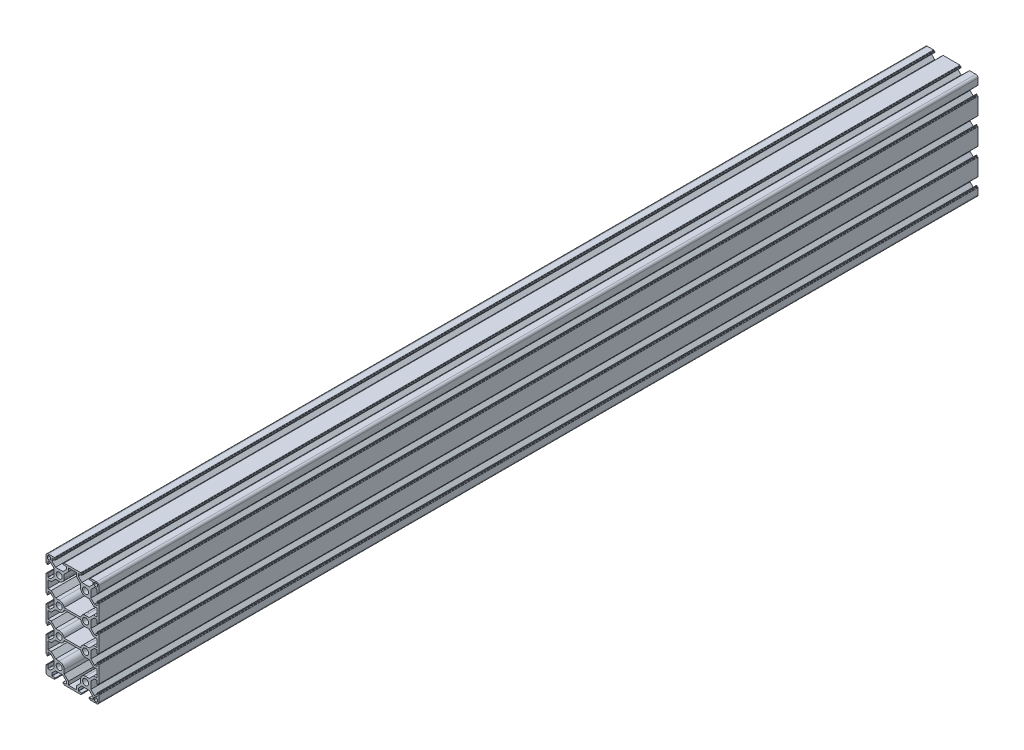
SolidWorks part; units mm, degrees
material "6063 T5"
ref_plane "Спереди" through (0, 0, 0) normal (0, 0, 1) x (1, 0, 0)
ref_plane "Сверху" through (0, 0, 0) normal (0, 1, 0) x (1, 0, 0)
ref_plane "Справа" through (0, 0, 0) normal (1, 0, 0) x (0, 0, -1)
sketch "Эскиз1" plane through (0, 0, 0) normal (0, 0, 1) x (1, 0, 0)
  line L0 (-34.4622, 45.0307) -> (-34.4622, -44.9693) construction
  line L1 (0, 45) -> (0, -45) construction
  line L2 (30, 0) -> (-30, 0) construction
  line L3 (-30, 38.25) -> (-30, 42.5)
  line L4 (-27.5, 45) -> (-23.25, 45)
  line L5 (4.5, 42.8) -> (-4.5, 42.8)
  line L6 (-27.35, 43.55) -> (-25.95, 43.55)
  line L7 (-28.55, 42.35) -> (-28.55, 40.95)
  line L8 (-27.35, 39.75) -> (-25.95, 39.75)
  line L9 (-24.75, 42.35) -> (-24.75, 40.95)
  line L10 (-4.5, 42.8) -> (-4.5, 38.9059)
  line L11 (-4.5, 38.9059) -> (-9.3, 34.1059)
  line L12 (-9.3, 34.1059) -> (-9.3, 30)
  line L13 (-15, 24.3) -> (-19.1059, 24.3)
  line L14 (-19.1059, 24.3) -> (-24.0559, 19.35)
  line L15 (-24.0559, 19.35) -> (-27.8, 19.35)
  line L16 (-27.8, 19.35) -> (-27.8, 10.65)
  line L17 (-27.8, 10.65) -> (-24.0559, 10.65)
  line L18 (-24.0559, 10.65) -> (-19.1059, 5.7)
  line L19 (-19.1059, 5.7) -> (-15, 5.7)
  line L20 (-9.4071, 1.1) -> (9.4071, 1.1)
  line L21 (-6.75, 45) -> (6.75, 45)
  line L22 (-30, 21.75) -> (-30, 8.25)
  line L23 (30, 21.75) -> (30, 8.25)
  line L24 (27.5, 45) -> (23.25, 45)
  line L25 (30, 38.25) -> (30, 42.5)
  line L26 (19.1059, 5.7) -> (15, 5.7)
  line L27 (24.0559, 10.65) -> (19.1059, 5.7)
  line L28 (27.8, 10.65) -> (24.0559, 10.65)
  line L29 (27.8, 19.35) -> (27.8, 10.65)
  line L30 (24.0559, 19.35) -> (27.8, 19.35)
  line L31 (19.1059, 24.3) -> (24.0559, 19.35)
  line L32 (15, 24.3) -> (19.1059, 24.3)
  line L33 (9.3, 34.1059) -> (9.3, 30)
  line L34 (4.5, 38.9059) -> (9.3, 34.1059)
  line L35 (4.5, 42.8) -> (4.5, 38.9059)
  line L36 (27.35, 43.55) -> (25.95, 43.55)
  line L37 (28.55, 42.35) -> (28.55, 40.95)
  line L38 (27.35, 39.75) -> (25.95, 39.75)
  line L39 (24.75, 42.35) -> (24.75, 40.95)
  line L40 (-9.4071, -28.9) -> (9.4071, -28.9)
  line L41 (30, -15) -> (45, -15) construction
  line L46 (30, -21.75) -> (30, -8.25)
  line L47 (-30, -21.75) -> (-30, -8.25)
  line L48 (-27.5, -75) -> (-23.25, -75)
  line L54 (15, -24.3) -> (19.1059, -24.3)
  line L55 (19.1059, -24.3) -> (24.0559, -19.35)
  line L56 (24.0559, -19.35) -> (27.8, -19.35)
  line L57 (27.8, -19.35) -> (27.8, -10.65)
  line L58 (27.8, -10.65) -> (24.0559, -10.65)
  line L59 (24.0559, -10.65) -> (19.1059, -5.7)
  line L60 (19.1059, -5.7) -> (15, -5.7)
  line L61 (-9.4071, -1.1) -> (9.4071, -1.1)
  line L62 (-19.1059, -5.7) -> (-15, -5.7)
  line L63 (-24.0559, -10.65) -> (-19.1059, -5.7)
  line L64 (-27.8, -10.65) -> (-24.0559, -10.65)
  line L65 (-27.8, -19.35) -> (-27.8, -10.65)
  line L66 (-24.0559, -19.35) -> (-27.8, -19.35)
  line L67 (-19.1059, -24.3) -> (-24.0559, -19.35)
  line L68 (-15, -24.3) -> (-19.1059, -24.3)
  line L75 (-30, -68.25) -> (-30, -72.5)
  line L76 (28.55, -72.35) -> (28.55, -70.95)
  line L77 (27.35, -73.55) -> (25.95, -73.55)
  line L78 (24.75, -72.35) -> (24.75, -70.95)
  line L79 (27.35, -69.75) -> (25.95, -69.75)
  line L80 (27.5, -75) -> (23.25, -75)
  line L81 (30, -68.25) -> (30, -72.5)
  line L82 (-6.75, -75) -> (6.75, -75)
  line L83 (27.8, -40.65) -> (24.0559, -40.65)
  line L84 (27.8, -49.35) -> (27.8, -40.65)
  line L85 (24.0559, -49.35) -> (27.8, -49.35)
  line L86 (19.1059, -54.3) -> (24.0559, -49.35)
  line L87 (15, -54.3) -> (19.1059, -54.3)
  line L88 (9.3, -64.1059) -> (9.3, -60)
  line L89 (4.5, -68.9059) -> (9.3, -64.1059)
  line L90 (4.5, -72.8) -> (4.5, -68.9059)
  line L91 (4.5, -72.8) -> (-4.5, -72.8)
  line L92 (-4.5, -72.8) -> (-4.5, -68.9059)
  line L93 (-4.5, -68.9059) -> (-9.3, -64.1059)
  line L94 (-9.3, -64.1059) -> (-9.3, -60)
  line L95 (-15, -54.3) -> (-19.1059, -54.3)
  line L96 (-19.1059, -54.3) -> (-24.0559, -49.35)
  line L97 (-24.0559, -49.35) -> (-27.8, -49.35)
  line L98 (-27.8, -49.35) -> (-27.8, -40.65)
  line L99 (-27.8, -40.65) -> (-24.0559, -40.65)
  line L100 (-24.0559, -40.65) -> (-19.1059, -35.7)
  line L101 (-19.1059, -35.7) -> (-15, -35.7)
  line L102 (-9.4071, -31.1) -> (9.4071, -31.1)
  line L103 (19.1059, -35.7) -> (15, -35.7)
  line L104 (24.0559, -40.65) -> (19.1059, -35.7)
  line L105 (-30, -51.75) -> (-30, -38.25)
  line L106 (30, -51.75) -> (30, -38.25)
  arc A0 (-30, 42.5) -> (-27.5, 45) centre (-27.5, 42.5) cw
  arc A1 (-28.55, 40.95) -> (-27.35, 39.75) centre (-27.35, 40.95) ccw
  arc A2 (-25.95, 39.75) -> (-24.75, 40.95) centre (-25.95, 40.95) ccw
  arc A3 (-25.95, 43.55) -> (-24.75, 42.35) centre (-25.95, 42.35) cw
  arc A4 (-27.35, 43.55) -> (-28.55, 42.35) centre (-27.35, 42.35) ccw
  circle A5 centre (-15, 30) radius 3.4
  arc A6 (-9.3, 30) -> (-15, 24.3) centre (-15, 30) cw
  arc A7 (-15, 5.7) -> (-9.4071, 1.1) centre (-15, 0) cw
  circle A8 centre (-15, 0) radius 3.4
  arc A9 (30, 42.5) -> (27.5, 45) centre (27.5, 42.5) ccw
  arc A10 (15, 5.7) -> (9.4071, 1.1) centre (15, 0) ccw
  arc A11 (9.3, 30) -> (15, 24.3) centre (15, 30) ccw
  circle A12 centre (15, 30) radius 3.4
  circle A13 centre (15, 0) radius 3.4
  arc A14 (25.95, 43.55) -> (24.75, 42.35) centre (25.95, 42.35) ccw
  arc A15 (27.35, 43.55) -> (28.55, 42.35) centre (27.35, 42.35) cw
  arc A16 (28.55, 40.95) -> (27.35, 39.75) centre (27.35, 40.95) cw
  arc A17 (25.95, 39.75) -> (24.75, 40.95) centre (25.95, 40.95) cw
  arc A18 (-15, -24.3) -> (-9.4071, -28.9) centre (-15, -30) cw
  circle A23 centre (-15, -30) radius 3.4
  circle A24 centre (15, -30) radius 3.4
  arc A26 (15, -5.7) -> (9.4071, -1.1) centre (15, 0) cw
  arc A27 (-15, -5.7) -> (-9.4071, -1.1) centre (-15, 0) ccw
  arc A33 (15, -24.3) -> (9.4071, -28.9) centre (15, -30) ccw
  arc A34 (-30, -72.5) -> (-27.5, -75) centre (-27.5, -72.5) ccw
  arc A35 (28.55, -70.95) -> (27.35, -69.75) centre (27.35, -70.95) ccw
  arc A36 (27.35, -73.55) -> (28.55, -72.35) centre (27.35, -72.35) ccw
  arc A37 (25.95, -73.55) -> (24.75, -72.35) centre (25.95, -72.35) cw
  arc A38 (25.95, -69.75) -> (24.75, -70.95) centre (25.95, -70.95) ccw
  arc A39 (30, -72.5) -> (27.5, -75) centre (27.5, -72.5) cw
  arc A40 (9.3, -60) -> (15, -54.3) centre (15, -60) cw
  arc A41 (-9.3, -60) -> (-15, -54.3) centre (-15, -60) ccw
  arc A42 (-15, -35.7) -> (-9.4071, -31.1) centre (-15, -30) ccw
  arc A43 (15, -35.7) -> (9.4071, -31.1) centre (15, -30) cw
  circle A44 centre (-15, -60) radius 3.4
  circle A45 centre (15, -60) radius 3.4
  point P22 (-24.75, 43.55)
  point P25 (-28.55, 43.55)
  point P63 (0, 1.1)
  point P72 (0, 42.8)
  point P174 (47.9891, -15)
  point P175 (-4.5, 38.9059)
  line B0 (-30, 8.25) -> (-30, 5.5)
  line B1 (-29.7, 5.2) -> (-29.3, 5.2)
  line B2 (-29, 4.9) -> (-29, 4.4)
  line B3 (-28.7, 4.1) -> (-28.3, 4.1)
  line B4 (-28, 4.4) -> (-28, 7.95)
  line B5 (-27.7, 8.25) -> (-25.05, 8.25)
  line B6 (-25.05, 8.25) -> (-21, 4.2)
  line B7 (-21, 0) -> (-30, 0) construction
  line B8 (-21, -4.2) -> (-21, 4.2)
  line B9 (-25.05, -8.25) -> (-21, -4.2)
  line B10 (-27.7, -8.25) -> (-25.05, -8.25)
  line B11 (-28, -4.4) -> (-28, -7.95)
  line B12 (-28.7, -4.1) -> (-28.3, -4.1)
  line B13 (-29, -4.9) -> (-29, -4.4)
  line B14 (-29.7, -5.2) -> (-29.3, -5.2)
  line B15 (-30, -8.25) -> (-30, -5.5)
  arc B16 (-28, 7.95) -> (-27.7, 8.25) centre (-27.7, 7.95) cw
  arc B17 (-28.3, 4.1) -> (-28, 4.4) centre (-28.3, 4.4) ccw
  arc B18 (-29, 4.4) -> (-28.7, 4.1) centre (-28.7, 4.4) ccw
  arc B19 (-29.3, 5.2) -> (-29, 4.9) centre (-29.3, 4.9) cw
  arc B20 (-30, 5.5) -> (-29.7, 5.2) centre (-29.7, 5.5) ccw
  arc B21 (-30, -5.5) -> (-29.7, -5.2) centre (-29.7, -5.5) cw
  arc B22 (-29.3, -5.2) -> (-29, -4.9) centre (-29.3, -4.9) ccw
  arc B23 (-29, -4.4) -> (-28.7, -4.1) centre (-28.7, -4.4) cw
  arc B24 (-28.3, -4.1) -> (-28, -4.4) centre (-28.3, -4.4) cw
  arc B25 (-28, -7.95) -> (-27.7, -8.25) centre (-27.7, -7.95) ccw
  line B26 (-30, 38.25) -> (-30, 35.5)
  line B27 (-29.7, 35.2) -> (-29.3, 35.2)
  line B28 (-29, 34.9) -> (-29, 34.4)
  line B29 (-28.7, 34.1) -> (-28.3, 34.1)
  line B30 (-28, 34.4) -> (-28, 37.95)
  line B31 (-27.7, 38.25) -> (-25.05, 38.25)
  line B32 (-25.05, 38.25) -> (-21, 34.2)
  line B33 (-21, 30) -> (-30, 30) construction
  line B34 (-21, 25.8) -> (-21, 34.2)
  line B35 (-25.05, 21.75) -> (-21, 25.8)
  line B36 (-27.7, 21.75) -> (-25.05, 21.75)
  line B37 (-28, 25.6) -> (-28, 22.05)
  line B38 (-28.7, 25.9) -> (-28.3, 25.9)
  line B39 (-29, 25.1) -> (-29, 25.6)
  line B40 (-29.7, 24.8) -> (-29.3, 24.8)
  line B41 (-30, 21.75) -> (-30, 24.5)
  arc B42 (-28, 37.95) -> (-27.7, 38.25) centre (-27.7, 37.95) cw
  arc B43 (-28.3, 34.1) -> (-28, 34.4) centre (-28.3, 34.4) ccw
  arc B44 (-29, 34.4) -> (-28.7, 34.1) centre (-28.7, 34.4) ccw
  arc B45 (-29.3, 35.2) -> (-29, 34.9) centre (-29.3, 34.9) cw
  arc B46 (-30, 35.5) -> (-29.7, 35.2) centre (-29.7, 35.5) ccw
  arc B47 (-30, 24.5) -> (-29.7, 24.8) centre (-29.7, 24.5) cw
  arc B48 (-29.3, 24.8) -> (-29, 25.1) centre (-29.3, 25.1) ccw
  arc B49 (-29, 25.6) -> (-28.7, 25.9) centre (-28.7, 25.6) cw
  arc B50 (-28.3, 25.9) -> (-28, 25.6) centre (-28.3, 25.6) cw
  arc B51 (-28, 22.05) -> (-27.7, 21.75) centre (-27.7, 22.05) ccw
  line B52 (-6.75, 45) -> (-9.5, 45)
  line B53 (-9.8, 44.7) -> (-9.8, 44.3)
  line B54 (-10.1, 44) -> (-10.6, 44)
  line B55 (-10.9, 43.7) -> (-10.9, 43.3)
  line B56 (-10.6, 43) -> (-7.05, 43)
  line B57 (-6.75, 42.7) -> (-6.75, 40.05)
  line B58 (-6.75, 40.05) -> (-10.8, 36)
  line B59 (-15, 36) -> (-15, 45) construction
  line B60 (-19.2, 36) -> (-10.8, 36)
  line B61 (-23.25, 40.05) -> (-19.2, 36)
  line B62 (-23.25, 42.7) -> (-23.25, 40.05)
  line B63 (-19.4, 43) -> (-22.95, 43)
  line B64 (-19.1, 43.7) -> (-19.1, 43.3)
  line B65 (-19.9, 44) -> (-19.4, 44)
  line B66 (-20.2, 44.7) -> (-20.2, 44.3)
  line B67 (-23.25, 45) -> (-20.5, 45)
  arc B68 (-7.05, 43) -> (-6.75, 42.7) centre (-7.05, 42.7) cw
  arc B69 (-10.9, 43.3) -> (-10.6, 43) centre (-10.6, 43.3) ccw
  arc B70 (-10.6, 44) -> (-10.9, 43.7) centre (-10.6, 43.7) ccw
  arc B71 (-9.8, 44.3) -> (-10.1, 44) centre (-10.1, 44.3) cw
  arc B72 (-9.5, 45) -> (-9.8, 44.7) centre (-9.5, 44.7) ccw
  arc B73 (-20.5, 45) -> (-20.2, 44.7) centre (-20.5, 44.7) cw
  arc B74 (-20.2, 44.3) -> (-19.9, 44) centre (-19.9, 44.3) ccw
  arc B75 (-19.4, 44) -> (-19.1, 43.7) centre (-19.4, 43.7) cw
  arc B76 (-19.1, 43.3) -> (-19.4, 43) centre (-19.4, 43.3) cw
  arc B77 (-22.95, 43) -> (-23.25, 42.7) centre (-22.95, 42.7) ccw
  line B78 (6.75, 45) -> (9.5, 45)
  line B79 (9.8, 44.7) -> (9.8, 44.3)
  line B80 (10.1, 44) -> (10.6, 44)
  line B81 (10.9, 43.7) -> (10.9, 43.3)
  line B82 (10.6, 43) -> (7.05, 43)
  line B83 (6.75, 42.7) -> (6.75, 40.05)
  line B84 (6.75, 40.05) -> (10.8, 36)
  line B85 (15, 36) -> (15, 45) construction
  line B86 (19.2, 36) -> (10.8, 36)
  line B87 (23.25, 40.05) -> (19.2, 36)
  line B88 (23.25, 42.7) -> (23.25, 40.05)
  line B89 (19.4, 43) -> (22.95, 43)
  line B90 (19.1, 43.7) -> (19.1, 43.3)
  line B91 (19.9, 44) -> (19.4, 44)
  line B92 (20.2, 44.7) -> (20.2, 44.3)
  line B93 (23.25, 45) -> (20.5, 45)
  arc B94 (7.05, 43) -> (6.75, 42.7) centre (7.05, 42.7) ccw
  arc B95 (10.9, 43.3) -> (10.6, 43) centre (10.6, 43.3) cw
  arc B96 (10.6, 44) -> (10.9, 43.7) centre (10.6, 43.7) cw
  arc B97 (9.8, 44.3) -> (10.1, 44) centre (10.1, 44.3) ccw
  arc B98 (9.5, 45) -> (9.8, 44.7) centre (9.5, 44.7) cw
  arc B99 (20.5, 45) -> (20.2, 44.7) centre (20.5, 44.7) ccw
  arc B100 (20.2, 44.3) -> (19.9, 44) centre (19.9, 44.3) cw
  arc B101 (19.4, 44) -> (19.1, 43.7) centre (19.4, 43.7) ccw
  arc B102 (19.1, 43.3) -> (19.4, 43) centre (19.4, 43.3) ccw
  arc B103 (22.95, 43) -> (23.25, 42.7) centre (22.95, 42.7) cw
  line B104 (30, 38.25) -> (30, 35.5)
  line B105 (29.7, 35.2) -> (29.3, 35.2)
  line B106 (29, 34.9) -> (29, 34.4)
  line B107 (28.7, 34.1) -> (28.3, 34.1)
  line B108 (28, 34.4) -> (28, 37.95)
  line B109 (27.7, 38.25) -> (25.05, 38.25)
  line B110 (25.05, 38.25) -> (21, 34.2)
  line B111 (21, 30) -> (30, 30) construction
  line B112 (21, 25.8) -> (21, 34.2)
  line B113 (25.05, 21.75) -> (21, 25.8)
  line B114 (27.7, 21.75) -> (25.05, 21.75)
  line B115 (28, 25.6) -> (28, 22.05)
  line B116 (28.7, 25.9) -> (28.3, 25.9)
  line B117 (29, 25.1) -> (29, 25.6)
  line B118 (29.7, 24.8) -> (29.3, 24.8)
  line B119 (30, 21.75) -> (30, 24.5)
  arc B120 (28, 37.95) -> (27.7, 38.25) centre (27.7, 37.95) ccw
  arc B121 (28.3, 34.1) -> (28, 34.4) centre (28.3, 34.4) cw
  arc B122 (29, 34.4) -> (28.7, 34.1) centre (28.7, 34.4) cw
  arc B123 (29.3, 35.2) -> (29, 34.9) centre (29.3, 34.9) ccw
  arc B124 (30, 35.5) -> (29.7, 35.2) centre (29.7, 35.5) cw
  arc B125 (30, 24.5) -> (29.7, 24.8) centre (29.7, 24.5) ccw
  arc B126 (29.3, 24.8) -> (29, 25.1) centre (29.3, 25.1) cw
  arc B127 (29, 25.6) -> (28.7, 25.9) centre (28.7, 25.6) ccw
  arc B128 (28.3, 25.9) -> (28, 25.6) centre (28.3, 25.6) ccw
  arc B129 (28, 22.05) -> (27.7, 21.75) centre (27.7, 22.05) cw
  line B130 (30, 8.25) -> (30, 5.5)
  line B131 (29.7, 5.2) -> (29.3, 5.2)
  line B132 (29, 4.9) -> (29, 4.4)
  line B133 (28.7, 4.1) -> (28.3, 4.1)
  line B134 (28, 4.4) -> (28, 7.95)
  line B135 (27.7, 8.25) -> (25.05, 8.25)
  line B136 (25.05, 8.25) -> (21, 4.2)
  line B137 (21, 0) -> (30, 0) construction
  line B138 (21, -4.2) -> (21, 4.2)
  line B139 (25.05, -8.25) -> (21, -4.2)
  line B140 (27.7, -8.25) -> (25.05, -8.25)
  line B141 (28, -4.4) -> (28, -7.95)
  line B142 (28.7, -4.1) -> (28.3, -4.1)
  line B143 (29, -4.9) -> (29, -4.4)
  line B144 (29.7, -5.2) -> (29.3, -5.2)
  line B145 (30, -8.25) -> (30, -5.5)
  arc B146 (28, 7.95) -> (27.7, 8.25) centre (27.7, 7.95) ccw
  arc B147 (28.3, 4.1) -> (28, 4.4) centre (28.3, 4.4) cw
  arc B148 (29, 4.4) -> (28.7, 4.1) centre (28.7, 4.4) cw
  arc B149 (29.3, 5.2) -> (29, 4.9) centre (29.3, 4.9) ccw
  arc B150 (30, 5.5) -> (29.7, 5.2) centre (29.7, 5.5) cw
  arc B151 (30, -5.5) -> (29.7, -5.2) centre (29.7, -5.5) ccw
  arc B152 (29.3, -5.2) -> (29, -4.9) centre (29.3, -4.9) cw
  arc B153 (29, -4.4) -> (28.7, -4.1) centre (28.7, -4.4) ccw
  arc B154 (28.3, -4.1) -> (28, -4.4) centre (28.3, -4.4) ccw
  arc B155 (28, -7.95) -> (27.7, -8.25) centre (27.7, -7.95) cw
  line B156 (-30, -38.25) -> (-30, -35.5)
  line B157 (-29.7, -35.2) -> (-29.3, -35.2)
  line B158 (-29, -34.9) -> (-29, -34.4)
  line B159 (-28.7, -34.1) -> (-28.3, -34.1)
  line B160 (-28, -34.4) -> (-28, -37.95)
  line B161 (-27.7, -38.25) -> (-25.05, -38.25)
  line B162 (-25.05, -38.25) -> (-21, -34.2)
  line B163 (-21, -30) -> (-30, -30) construction
  line B164 (-21, -25.8) -> (-21, -34.2)
  line B165 (-25.05, -21.75) -> (-21, -25.8)
  line B166 (-27.7, -21.75) -> (-25.05, -21.75)
  line B167 (-28, -25.6) -> (-28, -22.05)
  line B168 (-28.7, -25.9) -> (-28.3, -25.9)
  line B169 (-29, -25.1) -> (-29, -25.6)
  line B170 (-29.7, -24.8) -> (-29.3, -24.8)
  line B171 (-30, -21.75) -> (-30, -24.5)
  arc B172 (-28, -37.95) -> (-27.7, -38.25) centre (-27.7, -37.95) ccw
  arc B173 (-28.3, -34.1) -> (-28, -34.4) centre (-28.3, -34.4) cw
  arc B174 (-29, -34.4) -> (-28.7, -34.1) centre (-28.7, -34.4) cw
  arc B175 (-29.3, -35.2) -> (-29, -34.9) centre (-29.3, -34.9) ccw
  arc B176 (-30, -35.5) -> (-29.7, -35.2) centre (-29.7, -35.5) cw
  arc B177 (-30, -24.5) -> (-29.7, -24.8) centre (-29.7, -24.5) ccw
  arc B178 (-29.3, -24.8) -> (-29, -25.1) centre (-29.3, -25.1) cw
  arc B179 (-29, -25.6) -> (-28.7, -25.9) centre (-28.7, -25.6) ccw
  arc B180 (-28.3, -25.9) -> (-28, -25.6) centre (-28.3, -25.6) ccw
  arc B181 (-28, -22.05) -> (-27.7, -21.75) centre (-27.7, -22.05) cw
  line B182 (30, -38.25) -> (30, -35.5)
  line B183 (29.7, -35.2) -> (29.3, -35.2)
  line B184 (29, -34.9) -> (29, -34.4)
  line B185 (28.7, -34.1) -> (28.3, -34.1)
  line B186 (28, -34.4) -> (28, -37.95)
  line B187 (27.7, -38.25) -> (25.05, -38.25)
  line B188 (25.05, -38.25) -> (21, -34.2)
  line B189 (21, -30) -> (30, -30) construction
  line B190 (21, -25.8) -> (21, -34.2)
  line B191 (25.05, -21.75) -> (21, -25.8)
  line B192 (27.7, -21.75) -> (25.05, -21.75)
  line B193 (28, -25.6) -> (28, -22.05)
  line B194 (28.7, -25.9) -> (28.3, -25.9)
  line B195 (29, -25.1) -> (29, -25.6)
  line B196 (29.7, -24.8) -> (29.3, -24.8)
  line B197 (30, -21.75) -> (30, -24.5)
  arc B198 (28, -37.95) -> (27.7, -38.25) centre (27.7, -37.95) cw
  arc B199 (28.3, -34.1) -> (28, -34.4) centre (28.3, -34.4) ccw
  arc B200 (29, -34.4) -> (28.7, -34.1) centre (28.7, -34.4) ccw
  arc B201 (29.3, -35.2) -> (29, -34.9) centre (29.3, -34.9) cw
  arc B202 (30, -35.5) -> (29.7, -35.2) centre (29.7, -35.5) ccw
  arc B203 (30, -24.5) -> (29.7, -24.8) centre (29.7, -24.5) cw
  arc B204 (29.3, -24.8) -> (29, -25.1) centre (29.3, -25.1) ccw
  arc B205 (29, -25.6) -> (28.7, -25.9) centre (28.7, -25.6) cw
  arc B206 (28.3, -25.9) -> (28, -25.6) centre (28.3, -25.6) cw
  arc B207 (28, -22.05) -> (27.7, -21.75) centre (27.7, -22.05) ccw
  line B208 (6.75, -75) -> (9.5, -75)
  line B209 (9.8, -74.7) -> (9.8, -74.3)
  line B210 (10.1, -74) -> (10.6, -74)
  line B211 (10.9, -73.7) -> (10.9, -73.3)
  line B212 (10.6, -73) -> (7.05, -73)
  line B213 (6.75, -72.7) -> (6.75, -70.05)
  line B214 (6.75, -70.05) -> (10.8, -66)
  line B215 (15, -66) -> (15, -75) construction
  line B216 (19.2, -66) -> (10.8, -66)
  line B217 (23.25, -70.05) -> (19.2, -66)
  line B218 (23.25, -72.7) -> (23.25, -70.05)
  line B219 (19.4, -73) -> (22.95, -73)
  line B220 (19.1, -73.7) -> (19.1, -73.3)
  line B221 (19.9, -74) -> (19.4, -74)
  line B222 (20.2, -74.7) -> (20.2, -74.3)
  line B223 (23.25, -75) -> (20.5, -75)
  arc B224 (7.05, -73) -> (6.75, -72.7) centre (7.05, -72.7) cw
  arc B225 (10.9, -73.3) -> (10.6, -73) centre (10.6, -73.3) ccw
  arc B226 (10.6, -74) -> (10.9, -73.7) centre (10.6, -73.7) ccw
  arc B227 (9.8, -74.3) -> (10.1, -74) centre (10.1, -74.3) cw
  arc B228 (9.5, -75) -> (9.8, -74.7) centre (9.5, -74.7) ccw
  arc B229 (20.5, -75) -> (20.2, -74.7) centre (20.5, -74.7) cw
  arc B230 (20.2, -74.3) -> (19.9, -74) centre (19.9, -74.3) ccw
  arc B231 (19.4, -74) -> (19.1, -73.7) centre (19.4, -73.7) cw
  arc B232 (19.1, -73.3) -> (19.4, -73) centre (19.4, -73.3) cw
  arc B233 (22.95, -73) -> (23.25, -72.7) centre (22.95, -72.7) ccw
  line B234 (-6.75, -75) -> (-9.5, -75)
  line B235 (-9.8, -74.7) -> (-9.8, -74.3)
  line B236 (-10.1, -74) -> (-10.6, -74)
  line B237 (-10.9, -73.7) -> (-10.9, -73.3)
  line B238 (-10.6, -73) -> (-7.05, -73)
  line B239 (-6.75, -72.7) -> (-6.75, -70.05)
  line B240 (-6.75, -70.05) -> (-10.8, -66)
  line B241 (-15, -66) -> (-15, -75) construction
  line B242 (-19.2, -66) -> (-10.8, -66)
  line B243 (-23.25, -70.05) -> (-19.2, -66)
  line B244 (-23.25, -72.7) -> (-23.25, -70.05)
  line B245 (-19.4, -73) -> (-22.95, -73)
  line B246 (-19.1, -73.7) -> (-19.1, -73.3)
  line B247 (-19.9, -74) -> (-19.4, -74)
  line B248 (-20.2, -74.7) -> (-20.2, -74.3)
  line B249 (-23.25, -75) -> (-20.5, -75)
  arc B250 (-7.05, -73) -> (-6.75, -72.7) centre (-7.05, -72.7) ccw
  arc B251 (-10.9, -73.3) -> (-10.6, -73) centre (-10.6, -73.3) cw
  arc B252 (-10.6, -74) -> (-10.9, -73.7) centre (-10.6, -73.7) cw
  arc B253 (-9.8, -74.3) -> (-10.1, -74) centre (-10.1, -74.3) ccw
  arc B254 (-9.5, -75) -> (-9.8, -74.7) centre (-9.5, -74.7) cw
  arc B255 (-20.5, -75) -> (-20.2, -74.7) centre (-20.5, -74.7) ccw
  arc B256 (-20.2, -74.3) -> (-19.9, -74) centre (-19.9, -74.3) cw
  arc B257 (-19.4, -74) -> (-19.1, -73.7) centre (-19.4, -73.7) ccw
  arc B258 (-19.1, -73.3) -> (-19.4, -73) centre (-19.4, -73.3) ccw
  arc B259 (-22.95, -73) -> (-23.25, -72.7) centre (-22.95, -72.7) cw
  line B260 (30, -68.25) -> (30, -65.5)
  line B261 (29.7, -65.2) -> (29.3, -65.2)
  line B262 (29, -64.9) -> (29, -64.4)
  line B263 (28.7, -64.1) -> (28.3, -64.1)
  line B264 (28, -64.4) -> (28, -67.95)
  line B265 (27.7, -68.25) -> (25.05, -68.25)
  line B266 (25.05, -68.25) -> (21, -64.2)
  line B267 (21, -60) -> (30, -60) construction
  line B268 (21, -55.8) -> (21, -64.2)
  line B269 (25.05, -51.75) -> (21, -55.8)
  line B270 (27.7, -51.75) -> (25.05, -51.75)
  line B271 (28, -55.6) -> (28, -52.05)
  line B272 (28.7, -55.9) -> (28.3, -55.9)
  line B273 (29, -55.1) -> (29, -55.6)
  line B274 (29.7, -54.8) -> (29.3, -54.8)
  line B275 (30, -51.75) -> (30, -54.5)
  arc B276 (28, -67.95) -> (27.7, -68.25) centre (27.7, -67.95) cw
  arc B277 (28.3, -64.1) -> (28, -64.4) centre (28.3, -64.4) ccw
  arc B278 (29, -64.4) -> (28.7, -64.1) centre (28.7, -64.4) ccw
  arc B279 (29.3, -65.2) -> (29, -64.9) centre (29.3, -64.9) cw
  arc B280 (30, -65.5) -> (29.7, -65.2) centre (29.7, -65.5) ccw
  arc B281 (30, -54.5) -> (29.7, -54.8) centre (29.7, -54.5) cw
  arc B282 (29.3, -54.8) -> (29, -55.1) centre (29.3, -55.1) ccw
  arc B283 (29, -55.6) -> (28.7, -55.9) centre (28.7, -55.6) cw
  arc B284 (28.3, -55.9) -> (28, -55.6) centre (28.3, -55.6) cw
  arc B285 (28, -52.05) -> (27.7, -51.75) centre (27.7, -52.05) ccw
  line B286 (-30, -68.25) -> (-30, -65.5)
  line B287 (-29.7, -65.2) -> (-29.3, -65.2)
  line B288 (-29, -64.9) -> (-29, -64.4)
  line B289 (-28.7, -64.1) -> (-28.3, -64.1)
  line B290 (-28, -64.4) -> (-28, -67.95)
  line B291 (-27.7, -68.25) -> (-25.05, -68.25)
  line B292 (-25.05, -68.25) -> (-21, -64.2)
  line B293 (-21, -60) -> (-30, -60) construction
  line B294 (-21, -55.8) -> (-21, -64.2)
  line B295 (-25.05, -51.75) -> (-21, -55.8)
  line B296 (-27.7, -51.75) -> (-25.05, -51.75)
  line B297 (-28, -55.6) -> (-28, -52.05)
  line B298 (-28.7, -55.9) -> (-28.3, -55.9)
  line B299 (-29, -55.1) -> (-29, -55.6)
  line B300 (-29.7, -54.8) -> (-29.3, -54.8)
  line B301 (-30, -51.75) -> (-30, -54.5)
  arc B302 (-28, -67.95) -> (-27.7, -68.25) centre (-27.7, -67.95) ccw
  arc B303 (-28.3, -64.1) -> (-28, -64.4) centre (-28.3, -64.4) cw
  arc B304 (-29, -64.4) -> (-28.7, -64.1) centre (-28.7, -64.4) cw
  arc B305 (-29.3, -65.2) -> (-29, -64.9) centre (-29.3, -64.9) ccw
  arc B306 (-30, -65.5) -> (-29.7, -65.2) centre (-29.7, -65.5) cw
  arc B307 (-30, -54.5) -> (-29.7, -54.8) centre (-29.7, -54.5) ccw
  arc B308 (-29.3, -54.8) -> (-29, -55.1) centre (-29.3, -55.1) cw
  arc B309 (-29, -55.6) -> (-28.7, -55.9) centre (-28.7, -55.6) ccw
  arc B310 (-28.3, -55.9) -> (-28, -55.6) centre (-28.3, -55.6) ccw
  arc B311 (-28, -52.05) -> (-27.7, -51.75) centre (-27.7, -52.05) cw
  dimension "D6" = 2.5
  dimension "D10" = 1.2
  dimension "D11" = 6.8
  dimension "D17" = 5.7
  dimension "D1" = 90
  dimension "D2" = 90
  dimension "D3" = 60
  dimension "D4" = 30
  dimension "D5" = 15
  dimension "D7" = 1.5
  dimension "D8" = 1.5
  dimension "D9" = 3.8
  dimension "D12" = 2.2
  dimension "D13" = 4.5
  dimension "D14" = 2.4
  dimension "D15" = 2.4
  dimension "D16" = 2.4
  dimension "D18" = 2.2
  dimension "D19" = 2.4
  dimension "D20" = 2.4
  dimension "D21" = 1.1
  dimension "D22" = 1.1
  dimension "D23" = 120
sketch_block_instance "8B(16,5P_low)-1"
sketch_block "8B(16,5P_low)" parameters "D6"=0.3, "D1"=16.5, "D2"=8.4, "D3"=9, "D4"=45, "D5"=10.4, "D7"=2, "D8"=1, "D9"=8.2, "D10"=8.4
sketch_block_instance "8B(16,5P_low)-3"
sketch_block_instance "8B(16,5P_low)-4"
sketch_block_instance "8B(16,5P_low)-5"
sketch_block_instance "8B(16,5P_low)-6"
sketch_block_instance "8B(16,5P_low)-7"
sketch_block_instance "8B(16,5P_low)-21"
sketch_block_instance "8B(16,5P_low)-22"
sketch_block_instance "8B(16,5P_low)-24"
sketch_block_instance "8B(16,5P_low)-25"
sketch_block_instance "8B(16,5P_low)-26"
sketch_block_instance "8B(16,5P_low)-27"
extrude "Бобышка-Вытянуть1" add sketch "Эскиз1" along normal blind 1000
